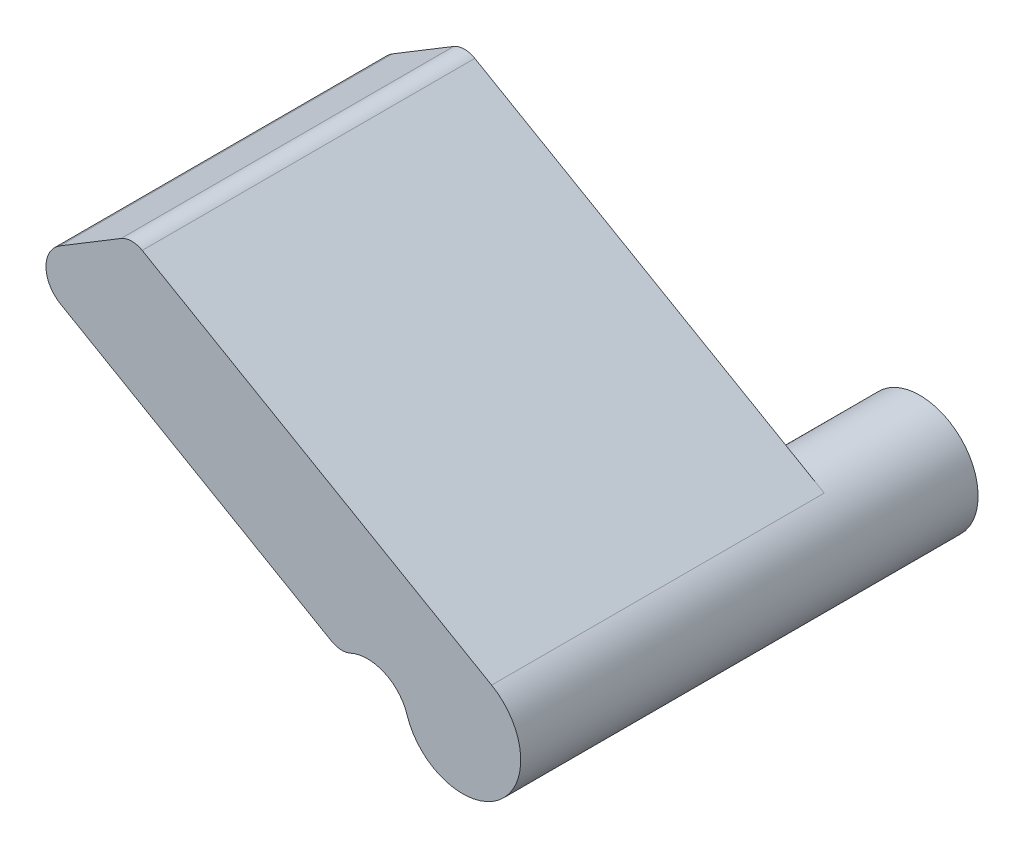
SolidWorks part; units mm, degrees
ref_plane "前视基准面" through (0, 0, 0) normal (0, 0, 1) x (1, 0, 0)
ref_plane "上视基准面" through (0, 0, 0) normal (0, 1, 0) x (1, 0, 0)
ref_plane "右视基准面" through (0, 0, 0) normal (1, 0, 0) x (0, 0, -1)
sketch "草图1" plane through (0, 0, 0) normal (0, 0, 1) x (1, 0, 0)
  line L0 (0.7, 1.2124) -> (-7.9603, 6.2124)
  line L1 (-7.9603, 6.2124) -> (-10.6942, 4.5577)
  line L2 (-10.6942, 4.5577) -> (-2.9, 0.0577)
  line L3 (0.7, 1.2124) -> (-5.1246, 1.2124) construction
  line L4 (0, 0) -> (0, 5.0845) construction
  line L5 (0, 0) -> (3.6976, 0) construction
  arc A0 (-1.3334, -0.4267) -> (0.7, 1.2124) centre (0, 0) ccw
  arc A1 (-2.9, 0.0577) -> (-1.3334, -0.4267) centre (-2.2858, -0.7314) cw
  dimension "D1" = 1
  dimension "D5" = 1.4
  dimension "D2" = 10
  dimension "D3" = 9
  dimension "D4" = 30
  dimension "D6" = 2.9
extrude "凸台-拉伸1" add sketch "草图1" along normal blind 8 contours L2 A1 A0 L0 L1
fillet "圆角1" radius 0.5 2 edges at (-7.9603, 6.2124, 4) (-2.9, 0.0577, 4)
fillet "圆角2" radius 0.7 1 edges at (-10.6942, 4.5577, 4)
sketch "草图2" plane through (0, 0, 0) normal (0, 0, -1) x (-1, 0, 0)
  circle A0 centre (0, 0) radius 1.4
  dimension "D1" = 2.8
extrude "凸台-拉伸2" add sketch "草图2" along normal blind 3
